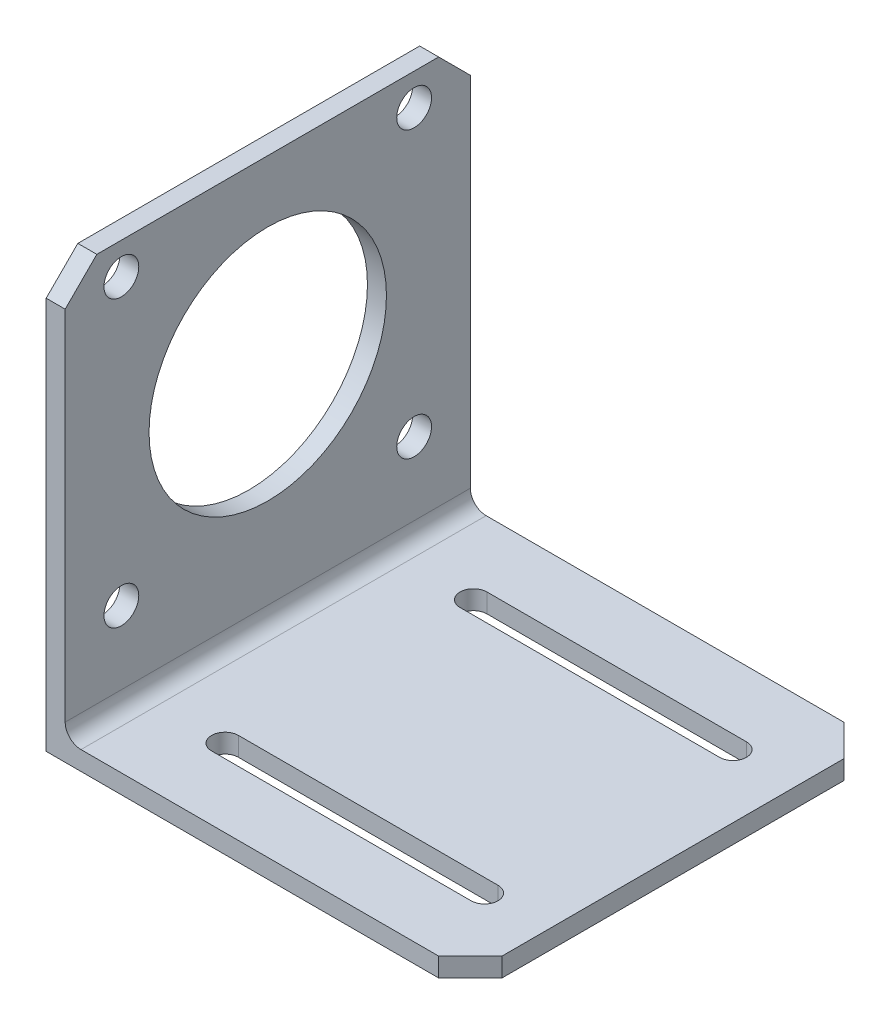
SolidWorks part; units mm, degrees
material "AISI 1020"
ref_plane "Front Plane" through (0, 0, 0) normal (0, 0, 1) x (1, 0, 0)
ref_plane "Top Plane" through (0, 0, 0) normal (0, 1, 0) x (1, 0, 0)
ref_plane "Right Plane" through (0, 0, 0) normal (1, 0, 0) x (0, 0, -1)
sketch "Sketch1" plane through (0, 0, 0) normal (0, 0, 1) x (1, 0, 0)
  line L1 (-1.524, 32.512) -> (1.524, 32.512)
  line L2 (-1.524, 32.512) -> (-1.524, -32.512)
  line L4 (1.524, 32.512) -> (1.524, -32.512)
  line L5 (-1.524, 32.512) -> (1.524, -32.512) construction
  line L6 (-1.524, -32.512) -> (1.524, 32.512) construction
  line L7 (1.524, -32.512) -> (66.548, -32.512)
  line L8 (-1.524, -32.512) -> (-1.524, -35.56)
  line L9 (-1.524, -35.56) -> (66.548, -35.56)
  line L10 (66.548, -32.512) -> (66.548, -35.56)
  point P0 (0, 0)
  dimension "D1" = 65.024
  dimension "D2" = 3.048
  dimension "D3" = 65.024
  dimension "D4" = 3.048
extrude "Boss-Extrude1" add sketch "Sketch1" against normal blind 65.024
sketch "Sketch2" plane through (0, -32.512, 0) normal (0, 1, 0) x (1, 0, 0)
  line L0 (66.548, 65.024) -> (66.548, 0) construction
  line L1 (14.732, 14.605) -> (56.388, 14.605)
  line L3 (14.732, 10.287) -> (56.388, 10.287)
  line L5 (14.732, 54.483) -> (56.388, 54.483)
  line L7 (14.732, 50.165) -> (56.388, 50.165)
  line L9 (66.548, 65.024) -> (1.524, 65.024) construction
  arc A0 (56.388, 14.605) -> (56.388, 10.287) centre (56.388, 12.446) cw
  arc A1 (14.732, 14.605) -> (14.732, 10.287) centre (14.732, 12.446) ccw
  arc A2 (56.388, 54.483) -> (56.388, 50.165) centre (56.388, 52.324) cw
  arc A3 (14.732, 50.165) -> (14.732, 54.483) centre (14.732, 52.324) cw
  point P12 (35.56, 50.165)
  point P13 (35.56, 14.605)
  dimension "D2" = 4.318
  dimension "D3" = 4.318
  dimension "D5" = 39.878
  dimension "D7" = 12.7
  dimension "D1" = 41.656
  dimension "D4" = 41.656
  dimension "D6" = 10.16
extrude "Cut-Extrude1" cut sketch "Sketch2" against normal blind 65.024
sketch "Sketch3" plane through (-1.524, 0, 0) normal (-1, 0, 0) x (0, 0, 1)
  line L1 (-65.024, 32.512) -> (0, 32.512) construction
  line L2 (0, 32.512) -> (0, -35.56) construction
  circle A0 centre (-32.512, 3.556) radius 19.05
  circle A1 centre (-56.007, -18.288) radius 2.794
  circle A2 centre (-9.017, -18.288) radius 2.794
  circle A3 centre (-9.017, 27.432) radius 2.794
  circle A4 centre (-56.007, 27.432) radius 2.794
  dimension "D1" = 38.1
  dimension "D2" = 5.588
  dimension "D3" = 5.588
  dimension "D4" = 5.588
  dimension "D5" = 5.588
  dimension "D7" = 23.495
  dimension "D8" = 46.99
  dimension "D9" = 23.495
  dimension "D10" = 45.72
  dimension "D6" = 46.99
  dimension "D11" = 28.956
  dimension "D12" = 32.512
  dimension "D13" = 23.876
extrude "Cut-Extrude2" cut sketch "Sketch3" against normal blind 65.024
fillet "Fillet1" radius 2.54 1 edges at (1.524, -32.512, -32.512)
chamfer "Chamfer1" distance 5.08 angle 45 4 edges at (0, 32.512, 0) (0, 32.512, -65.024) (66.548, -34.036, -65.024) (66.548, -34.036, 0)
